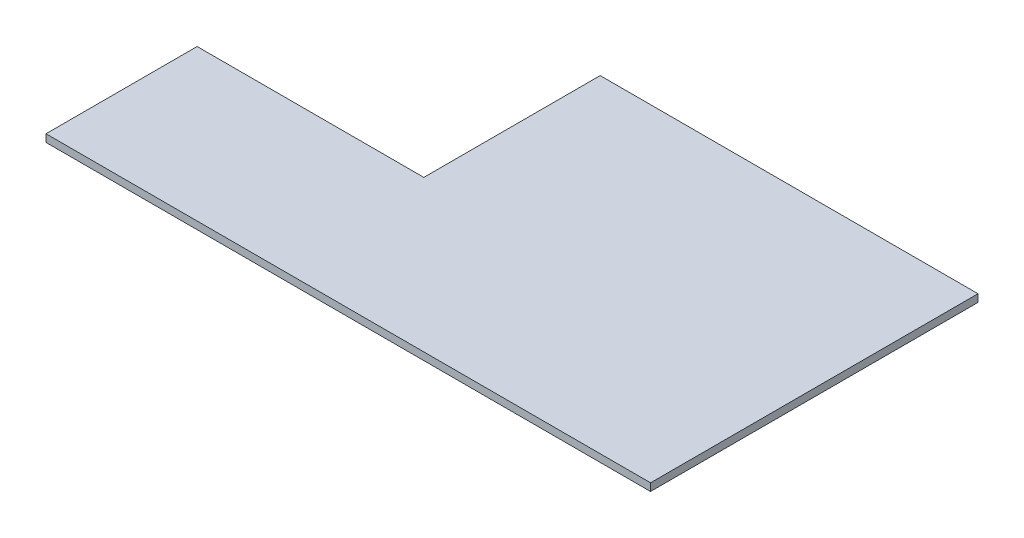
SolidWorks part; units mm, degrees
ref_plane "Front Plane" through (0, 0, 0) normal (0, 0, 1) x (1, 0, 0)
ref_plane "Top Plane" through (0, 0, 0) normal (0, 1, 0) x (1, 0, 0)
ref_plane "Right Plane" through (0, 0, 0) normal (1, 0, 0) x (0, 0, -1)
sketch "Sketch1" plane through (0, 0, 0) normal (0, 1, 0) x (1, 0, 0)
  line L1 (-120, 3.4261) -> (120, 3.4261)
  line L2 (-120, 3.4261) -> (-120, 63.4261)
  line L3 (-120, 63.4261) -> (-30, 63.4261)
  line L4 (120, 3.4261) -> (120, 130.2782)
  line L8 (120, 130.2782) -> (120, 133.4261)
  line L9 (120, 133.4261) -> (-30, 133.4261)
  line L10 (-30, 63.4261) -> (-30, 133.4261)
  point P0 (0, 0)
  dimension "D1" = 240
  dimension "D2" = 90
  dimension "D3" = 70
  dimension "D4" = 60
extrude "Boss-Extrude1" add sketch "Sketch1" along normal blind 3
